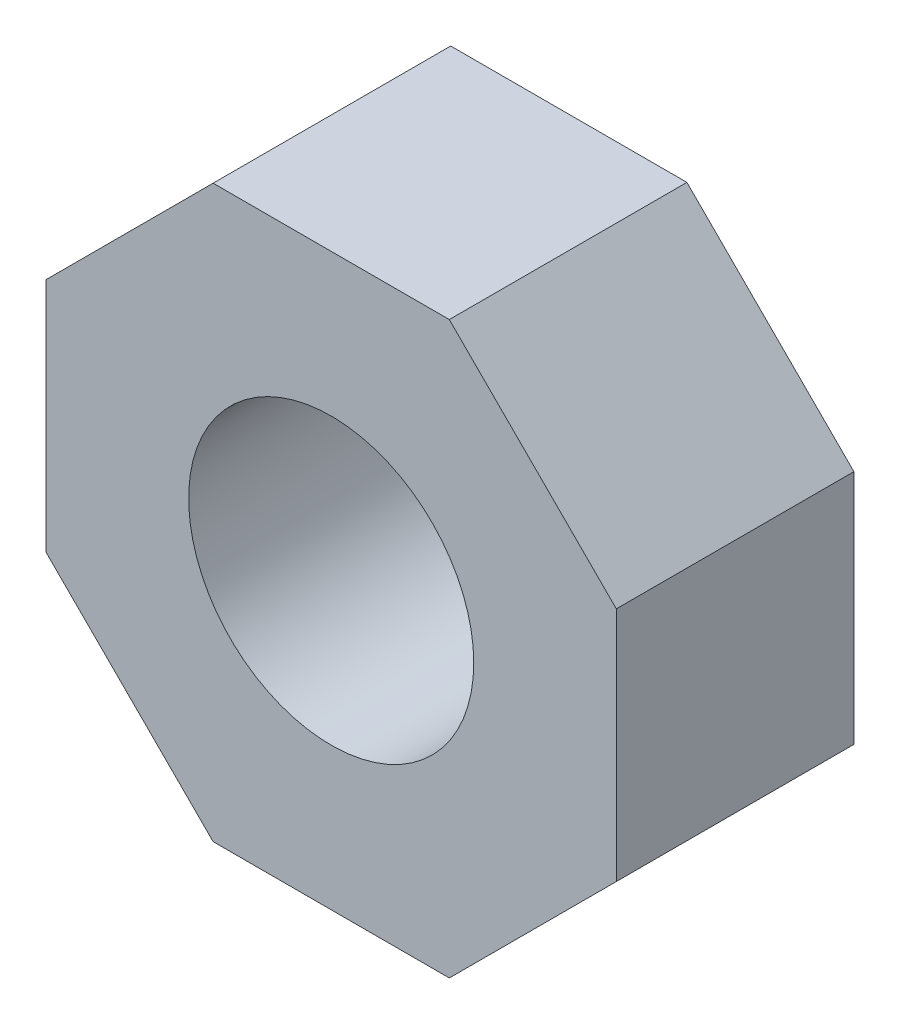
SolidWorks part; units mm, degrees
ref_plane "Plan de face" through (0, 0, 0) normal (0, 0, 1) x (1, 0, 0)
ref_plane "Plan de dessus" through (0, 0, 0) normal (0, 1, 0) x (1, 0, 0)
ref_plane "Plan de droite" through (0, 0, 0) normal (1, 0, 0) x (0, 0, -1)
sketch "Esquisse1" plane through (0, 0, 0) normal (0, 0, 1) x (1, 0, 0)
  line L0 (0, 0) -> (6, 0) construction
  line L1 (6, 0) -> (-6, 0) construction
  line L2 (-4.2426, 4.2426) -> (-6, 2.4853)
  line L3 (6, 6) -> (6, -6) construction
  line L4 (-6, -6) -> (6, 6) construction
  line L5 (6, 6) -> (-6, 6) construction
  line L6 (0, 0) -> (0, 6) construction
  line L7 (0, 6) -> (0, -6) construction
  line L8 (6, -6) -> (-6, 6) construction
  line L9 (0, 0) -> (-4.2426, -4.2426) construction
  line L10 (-4.2426, -4.2426) -> (0, 0) construction
  line L11 (0, 0) -> (4.2426, -4.2426) construction
  line L12 (-6, 6) -> (0, 6) construction
  line L13 (0, 6) -> (6, 6) construction
  line L15 (6, -6) -> (-6, -6) construction
  line L16 (-6, -6) -> (-6, 6) construction
  line L17 (4.2426, -4.2426) -> (0, 0) construction
  line L18 (0, 0) -> (4.2426, 4.2426) construction
  line L19 (4.2426, 4.2426) -> (0, 0) construction
  line L20 (0, 0) -> (-4.2426, 4.2426) construction
  line L21 (4.2426, 4.2426) -> (2.4853, 6)
  line L22 (-6, 2.4853) -> (-6, 0)
  line L23 (-4.2426, 4.2426) -> (-2.4853, 6)
  line L24 (2.4853, 6) -> (6, 2.4853)
  line L25 (4.2426, -4.2426) -> (6, -2.4853)
  line L26 (6, -2.4853) -> (2.4853, -6)
  line L27 (-2.4853, 6) -> (2.4853, 6)
  line L28 (-4.2426, -4.2426) -> (-2.4853, -6)
  line L29 (-2.4853, -6) -> (2.4853, -6)
  line L30 (-4.2426, -4.2426) -> (-6, -2.4853)
  line L31 (6, 2.4853) -> (6, -2.4853)
  line L32 (6, -2.4853) -> (2.4853, -6)
  line L33 (-6, -2.4853) -> (-6, 0)
  line L34 (6, 2.4853) -> (6, -2.4853)
  circle A0 centre (0, 0) radius 6 construction
  circle A1 centre (0, 0) radius 3
extrude "Boss.-Extru.1" add sketch "Esquisse1" along normal blind 5
